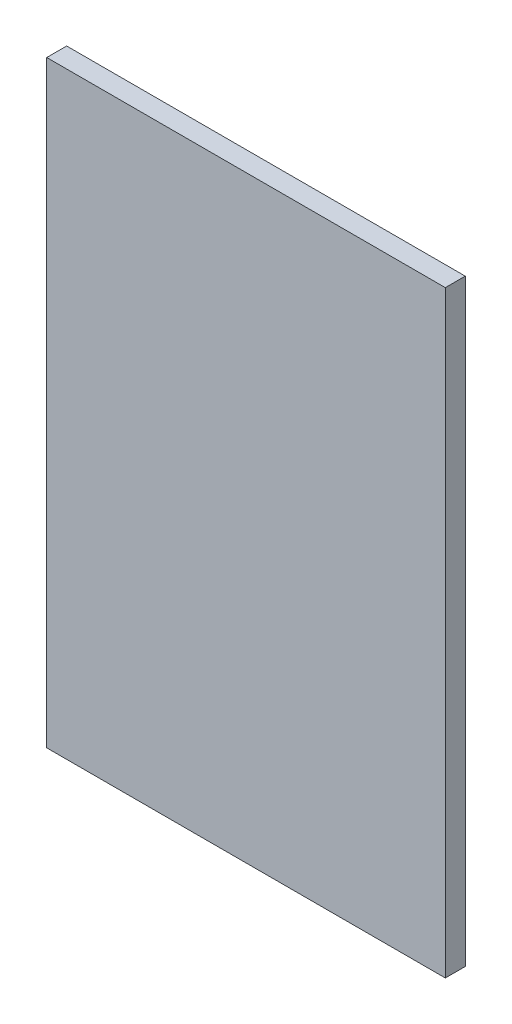
SolidWorks part; units mm, degrees
ref_plane "Front Plane" through (0, 0, 0) normal (0, 0, 1) x (1, 0, 0)
ref_plane "Top Plane" through (0, 0, 0) normal (0, 1, 0) x (1, 0, 0)
ref_plane "Right Plane" through (0, 0, 0) normal (1, 0, 0) x (0, 0, -1)
sketch "Sketch1" plane through (0, 0, 0) normal (0, 0, 1) x (1, 0, 0)
  line L1 (0, 0) -> (200, 0)
  line L2 (0, 0) -> (0, 300)
  line L3 (0, 300) -> (200, 300)
  line L4 (200, 0) -> (200, 300)
  dimension "D1" = 200
  dimension "D2" = 300
extrude "Boss-Extrude1" add sketch "Sketch1" along normal blind 10
sketch "Sketch2" plane through (0, 0, 10) normal (0, 0, 1) x (1, 0, 0)
  line L0 (100, 300) -> (100, 0) construction
  line L1 (200, 300) -> (0, 300) construction
  line L2 (0, 0) -> (200, 0) construction
sketch "Sketch3" plane through (0, 0, 10) normal (0, 0, 1) x (1, 0, 0)
  circle A0 centre (100, 99.6059) radius 4.45
  circle A3 centre (100, 139.6059) radius 4.45
  dimension "D1" = 8.9
  dimension "D2" = 8.9
extrude "Cut-Extrude1" [suppressed] cut sketch "Sketch3" against normal blind 10
sketch "Sketch5" plane through (0, 0, 10) normal (0, 0, 1) x (1, 0, 0)
  line L15 (91.536, 226.6059) -> (43.8, 226.6059)
  line L16 (29.8, 212.6059) -> (29.8, 153.11)
  line L17 (32.4795, 143.11) -> (66.2568, 84.6059)
  line L24 (74.9171, 79.6059) -> (125.0829, 79.6059)
  line L25 (133.7432, 84.6059) -> (167.5205, 143.11)
  line L26 (170.2, 153.11) -> (170.2, 212.6059)
  line L27 (156.2, 226.6059) -> (108.464, 226.6059)
  arc A12 (66.2568, 84.6059) -> (74.9171, 79.6059) centre (74.9171, 89.6059) ccw
  arc A15 (100, 223.7576) -> (91.536, 226.6059) centre (91.536, 212.6059) ccw
  arc A16 (43.8, 226.6059) -> (29.8, 212.6059) centre (43.8, 212.6059) ccw
  arc A17 (29.8, 153.11) -> (32.4795, 143.11) centre (49.8, 153.11) ccw
  arc A25 (125.0829, 79.6059) -> (133.7432, 84.6059) centre (125.0829, 89.6059) ccw
  arc A26 (167.5205, 143.11) -> (170.2, 153.11) centre (150.2, 153.11) ccw
  arc A27 (170.2, 212.6059) -> (156.2, 226.6059) centre (156.2, 212.6059) ccw
  arc A28 (108.464, 226.6059) -> (100, 223.7576) centre (108.464, 212.6059) ccw
extrude "Cut-Extrude2" [suppressed] cut sketch "Sketch5" against normal blind 2
ref_plane "Plane1" through (0, 0, 9.5) normal (0, 0, 1) x (1, 0, 0)
